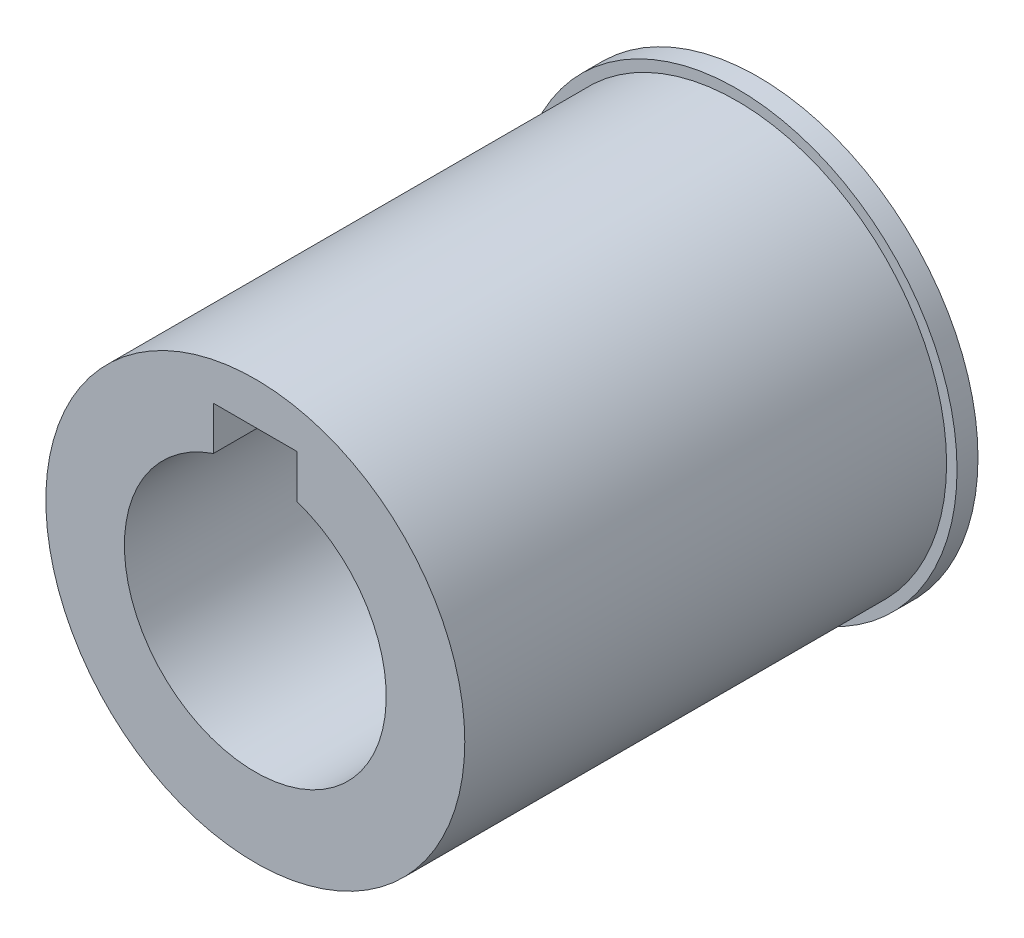
SolidWorks part; units mm, degrees
material "6061 Alloy"
ref_plane "Front Plane" through (0, 0, 0) normal (0, 0, 1) x (1, 0, 0)
ref_plane "Top Plane" through (0, 0, 0) normal (0, 1, 0) x (1, 0, 0)
ref_plane "Right Plane" through (0, 0, 0) normal (1, 0, 0) x (0, 0, -1)
sketch "Sketch1" plane through (0, 0, 0) normal (0, 0, 1) x (1, 0, 0)
  circle A0 centre (0, 0) radius 21
  dimension "D1" = 42
extrude "Boss-Extrude1" add sketch "Sketch1" along normal blind 2
sketch "Sketch2" plane through (0, 0, 2) normal (0, 0, 1) x (1, 0, 0)
  circle A0 centre (0, 0) radius 20
  dimension "D1" = 40
extrude "Boss-Extrude2" add sketch "Sketch2" along normal blind 46
sketch "Sketch3" plane through (0, 0, 0) normal (0, 0, -1) x (-1, 0, 0)
  circle A0 centre (0, 0) radius 12.5
  dimension "D1" = 25
extrude "Cut-Extrude1" cut sketch "Sketch3" against normal through all
sketch "Sketch4" plane through (0, 0, 0) normal (0, 0, -1) x (-1, 0, 0)
  line L0 (0, 1.1) -> (0, -1.1) construction
  line L1 (-4, 9) -> (4, 9)
  line L2 (-4, 9) -> (-4, 16)
  line L3 (-4, 16) -> (4, 16)
  line L4 (4, 9) -> (4, 16)
  line L5 (-4, 9) -> (4, 16) construction
  line L6 (-4, 16) -> (4, 9) construction
  circle A0 centre (0, 0) radius 12.5 construction
  point P0 (0, 12.5)
  dimension "D1" = 7
  dimension "D2" = 8
extrude "Cut-Extrude2" cut sketch "Sketch4" against normal up to surface (48 mm away) up to face at (-12.5, 0, 48)
